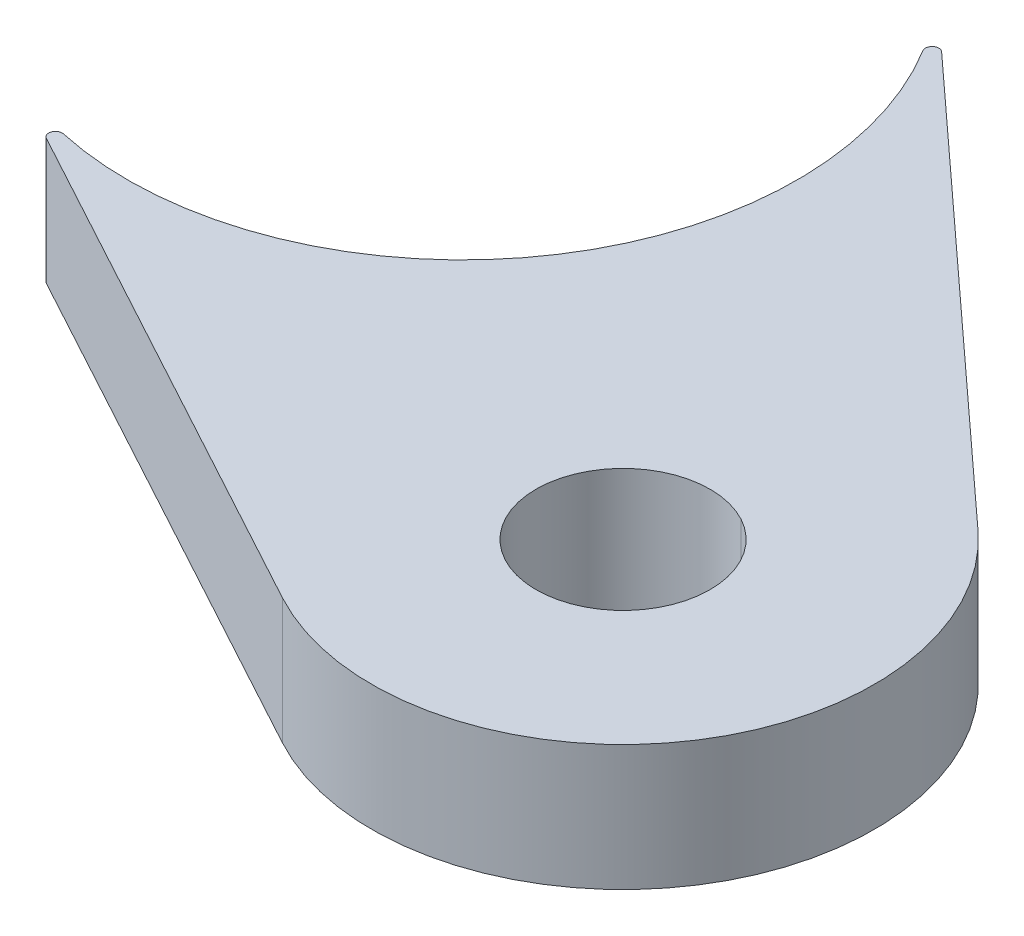
SolidWorks part; units mm, degrees
material "AISI 4130 Steel, annealed at 865C"
ref_plane "X-Y Datum" through (0, 0, 0) normal (0, 0, 1) x (1, 0, 0)
ref_plane "X-Z Datum" through (0, 0, 0) normal (0, 1, 0) x (1, 0, 0)
ref_plane "Y-Z Datum" through (0, 0, 0) normal (1, 0, 0) x (0, 0, -1)
sketch "Sketch1" plane through (0, 0, 0) normal (0, 1, 0) x (1, 0, 0)
  line L0 (16.6587, -23.4844) -> (-6.0555, -11.1634)
  line L1 (27.6336, -8.0878) -> (8.5778, 9.3654)
  circle A2 centre (21.2003, -15.1119) radius 3.3
  circle A3 centre (0, 0) radius 12.7 construction
  circle A4 centre (21.2003, -15.1119) radius 9.525 construction
  arc A6 (27.6336, -8.0878) -> (16.6587, -23.4844) centre (21.2003, -15.1119) cw
  arc A7 (-6.0555, -11.1634) -> (8.5778, 9.3654) centre (0, 0) ccw
  dimension "D3" = 25.4
  dimension "D4" = 19.05
  dimension "D5" = 6.6
  dimension "D1" = 26.035
extrude "Boss-Extrude1" add sketch "Sketch1" along normal blind 4.7625
fillet "Fillet1" radius 0.254 2 edges at (8.5778, 2.3813, -9.3654) (-6.0555, 2.3813, 11.1634)
ref_point "Point1"
ref_plane "Plane1" through (22.7141, 0, 12.3211) normal (0.879, 0, 0.4768) x (0.4768, 0, -0.879)
split line "Split Line1"
